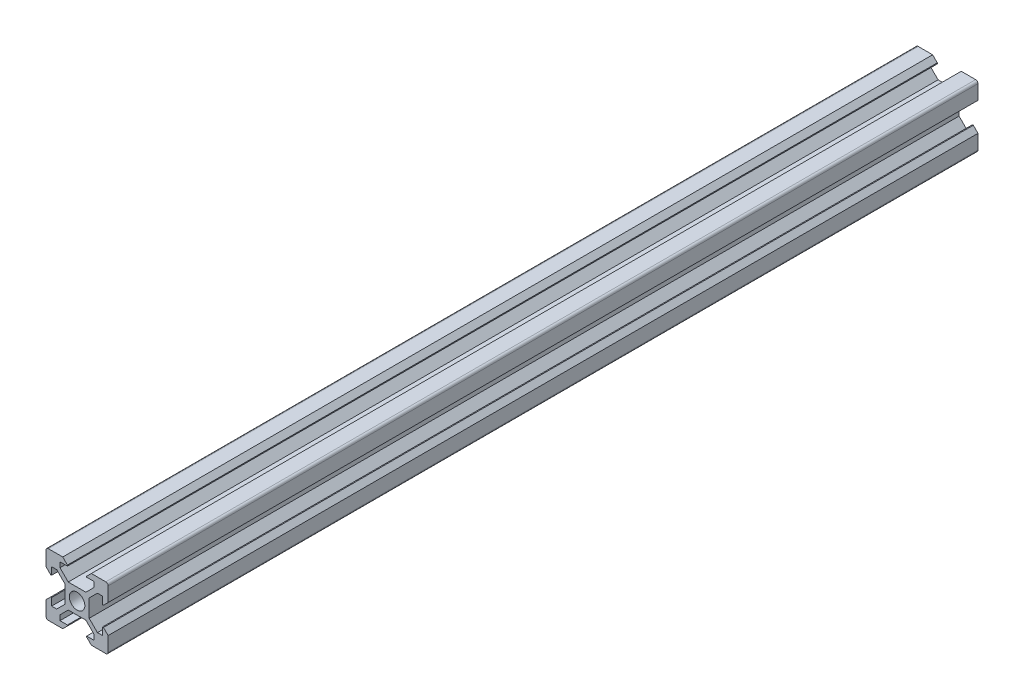
SolidWorks part; units mm, degrees
other "Markup1"
sketch "Sketch1" plane through (10, 10, 480) normal (0.5774, 0.5773, 0.5774) x (0.7071, 0, -0.7071)
ref_plane "Alzado" through (0, 0, 0) normal (0, 0, 1) x (1, 0, 0)
ref_plane "Planta" through (0, 0, 0) normal (0, 1, 0) x (1, 0, 0)
ref_plane "Vista lateral" through (0, 0, 0) normal (1, 0, 0) x (0, 0, -1)
sketch "Croquis1" plane through (0, 0, 0) normal (0, 0, 1) x (1, 0, 0)
  line L0 (-4.6, 10) -> (-3.1, 8.5)
  line L3 (-4.6, 10) -> (-9.25, 10)
  line L5 (-3.1, 8.5) -> (-3.1, 8.2)
  line L6 (-3.1, 8.2) -> (-5.5, 8.2)
  line L7 (-5.5, 8.2) -> (-5.5, 6.5607)
  line L8 (-5.5, 6.5607) -> (-2.84, 3.9007)
  line L9 (-2.84, 3.9007) -> (0, 3.9007)
  line L10 (0, 0) -> (-15.3499, 15.3499) construction
  line L11 (-3.9007, 2.84) -> (-3.9007, 0)
  line L12 (-6.5607, 5.5) -> (-3.9007, 2.84)
  line L13 (-8.2, 5.5) -> (-6.5607, 5.5)
  line L14 (-8.2, 3.1) -> (-8.2, 5.5)
  line L15 (-8.5, 3.1) -> (-8.2, 3.1)
  line L16 (-10, 4.6) -> (-10, 9.25)
  line L17 (-10, 4.6) -> (-8.5, 3.1)
  line L18 (10, 4.6) -> (8.5, 3.1)
  line L19 (10, 4.6) -> (10, 9.25)
  line L20 (8.5, 3.1) -> (8.2, 3.1)
  line L21 (8.2, 3.1) -> (8.2, 5.5)
  line L22 (8.2, 5.5) -> (6.5607, 5.5)
  line L23 (6.5607, 5.5) -> (3.9007, 2.84)
  line L24 (3.9007, 2.84) -> (3.9007, 0)
  line L25 (5.5, 6.5607) -> (2.84, 3.9007)
  line L26 (5.5, 8.2) -> (5.5, 6.5607)
  line L27 (3.1, 8.2) -> (5.5, 8.2)
  line L28 (3.1, 8.5) -> (3.1, 8.2)
  line L29 (4.6, 10) -> (9.25, 10)
  line L30 (4.6, 10) -> (3.1, 8.5)
  line L31 (2.84, 3.9007) -> (0, 3.9007)
  line L32 (4.6, -10) -> (3.1, -8.5)
  line L33 (4.6, -10) -> (9.25, -10)
  line L34 (3.1, -8.5) -> (3.1, -8.2)
  line L35 (3.1, -8.2) -> (5.5, -8.2)
  line L36 (5.5, -8.2) -> (5.5, -6.5607)
  line L37 (5.5, -6.5607) -> (2.84, -3.9007)
  line L38 (2.84, -3.9007) -> (0, -3.9007)
  line L39 (6.5607, -5.5) -> (3.9007, -2.84)
  line L40 (8.2, -5.5) -> (6.5607, -5.5)
  line L41 (8.2, -3.1) -> (8.2, -5.5)
  line L42 (8.5, -3.1) -> (8.2, -3.1)
  line L43 (10, -4.6) -> (10, -9.25)
  line L44 (10, -4.6) -> (8.5, -3.1)
  line L45 (3.9007, -2.84) -> (3.9007, 0)
  line L46 (-10, -4.6) -> (-8.5, -3.1)
  line L47 (-10, -4.6) -> (-10, -9.25)
  line L48 (-8.5, -3.1) -> (-8.2, -3.1)
  line L49 (-8.2, -3.1) -> (-8.2, -5.5)
  line L50 (-8.2, -5.5) -> (-6.5607, -5.5)
  line L51 (-6.5607, -5.5) -> (-3.9007, -2.84)
  line L52 (-3.9007, -2.84) -> (-3.9007, 0)
  line L53 (-5.5, -6.5607) -> (-2.84, -3.9007)
  line L54 (-5.5, -8.2) -> (-5.5, -6.5607)
  line L55 (-3.1, -8.2) -> (-5.5, -8.2)
  line L56 (-3.1, -8.5) -> (-3.1, -8.2)
  line L57 (-4.6, -10) -> (-9.25, -10)
  line L58 (-4.6, -10) -> (-3.1, -8.5)
  line L59 (-2.84, -3.9007) -> (0, -3.9007)
  circle A0 centre (0, 0) radius 2.5
  arc A1 (-9.25, 10) -> (-10, 9.25) centre (-9.25, 9.25) ccw
  arc A2 (10, 9.25) -> (9.25, 10) centre (9.25, 9.25) ccw
  arc A3 (9.25, -10) -> (10, -9.25) centre (9.25, -9.25) ccw
  arc A4 (-10, -9.25) -> (-9.25, -10) centre (-9.25, -9.25) ccw
  point P18 (-10, 10)
  point P37 (10, 10)
  point P55 (10, -10)
  point P73 (-10, -10)
  point P79 (0, 0)
  dimension "D1" = 5
  dimension "D5" = 0.75
  dimension "D2" = 10
  dimension "D3" = 10
  dimension "D4" = 4.6
  dimension "D6" = 5.5
  dimension "D7" = 135
  dimension "D8" = 0.75
  dimension "D9" = 225
  dimension "D10" = 2.84
  dimension "D11" = 1.8
  dimension "D12" = 3.1
  dimension "D13" = 4
extrude "Saliente-Extruir1" add sketch "Croquis1" along normal blind 280
